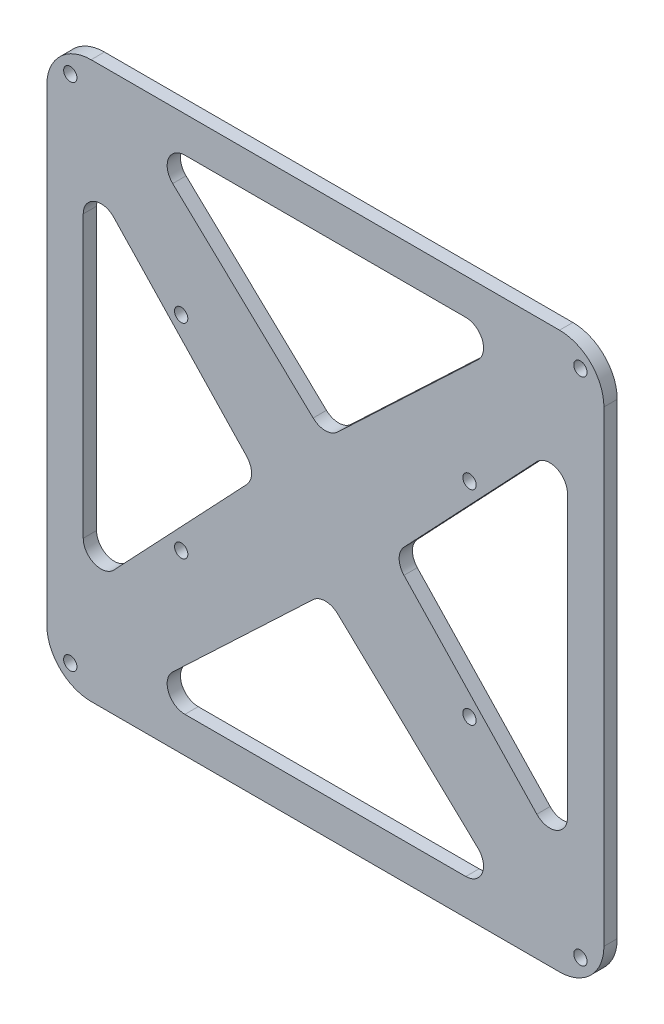
SolidWorks part; units mm, degrees
ref_plane "前视基准面" through (0, 0, 0) normal (0, 0, 1) x (1, 0, 0)
ref_plane "上视基准面" through (0, 0, 0) normal (0, 1, 0) x (1, 0, 0)
ref_plane "右视基准面" through (0, 0, 0) normal (1, 0, 0) x (0, 0, -1)
sketch "草图1" plane through (0, 0, 0) normal (0, 0, 1) x (1, 0, 0)
  line L0 (0, -62.65) -> (125.6, -62.65) construction
  line L1 (0, 0) -> (125.6, 0)
  line L2 (0, 0) -> (0, -125.3)
  line L3 (0, -125.3) -> (125.6, -125.3)
  line L4 (125.6, 0) -> (125.6, -125.3)
  line L5 (62.8, 0) -> (62.8, -125.3) construction
  line L6 (21.0898, -117.2294) -> (104.5102, -117.2294)
  line L7 (30.3, -85.65) -> (95.3, -85.65) construction
  line L8 (30.3, -85.65) -> (30.3, -39.65) construction
  line L9 (30.3, -39.65) -> (95.3, -39.65) construction
  line L10 (95.3, -85.65) -> (95.3, -39.65) construction
  line L11 (30.3, -85.65) -> (95.3, -39.65) construction
  line L12 (30.3, -39.65) -> (95.3, -85.65) construction
  line L13 (104.5102, -117.2294) -> (62.8, -77.7781)
  line L14 (62.8, -77.7781) -> (21.0898, -117.2294)
  line L15 (8.2206, -104.3602) -> (47.6719, -62.65)
  line L16 (8.2206, -20.9398) -> (8.2206, -104.3602)
  line L17 (47.6719, -62.65) -> (8.2206, -20.9398)
  line L18 (21.0898, -8.0706) -> (62.8, -47.5219)
  line L19 (104.5102, -8.0706) -> (21.0898, -8.0706)
  line L20 (62.8, -47.5219) -> (104.5102, -8.0706)
  line L21 (117.3794, -20.9398) -> (77.9281, -62.65)
  line L22 (117.3794, -104.3602) -> (117.3794, -20.9398)
  line L23 (77.9281, -62.65) -> (117.3794, -104.3602)
  line L25 (120.3, -5.15) -> (5.3, -5.15) construction
  line L26 (120.3, -5.15) -> (120.3, -120.15) construction
  line L27 (120.3, -120.15) -> (5.3, -120.15) construction
  line L28 (5.3, -5.15) -> (5.3, -120.15) construction
  line L29 (120.3, -5.15) -> (5.3, -120.15) construction
  line L30 (120.3, -120.15) -> (5.3, -5.15) construction
  circle A0 centre (30.3, -39.65) radius 1.5
  circle A1 centre (95.3, -39.65) radius 1.5
  circle A2 centre (95.3, -85.65) radius 1.5
  circle A3 centre (30.3, -85.65) radius 1.5
  circle A4 centre (120.3, -120.15) radius 1.5
  circle A5 centre (5.3, -120.15) radius 1.5
  circle A6 centre (5.3, -5.15) radius 1.5
  circle A7 centre (120.3, -5.15) radius 1.5
  point P9 (62.8, -62.65)
  point P22 (62.8, -117.2294)
  point P41 (62.8, -62.65)
  dimension "D5" = 3
  dimension "D6" = 3
  dimension "D7" = 3
  dimension "D8" = 3
  dimension "D12" = 3
  dimension "D13" = 3
  dimension "D14" = 3
  dimension "D15" = 3
  dimension "D1" = 125.3
  dimension "D2" = 125.6
  dimension "D3" = 65
  dimension "D4" = 46
  dimension "D10" = 115
  dimension "D11" = 115
  dimension "D9" = 4
extrude "凸台-拉伸1" add sketch "草图1" along normal blind 3
fillet "圆角1" radius 10 4 edges at (0, -125.3, 1.5) (125.6, -125.3, 1.5) (125.6, 0, 1.5) (0, 0, 1.5)
fillet "圆角2" radius 4 12 edges at (77.9281, -62.65, 1.5) (117.3794, -104.3602, 1.5) (104.5102, -117.2294, 1.5) (104.5102, -8.0706, 1.5) (117.3794, -20.9398, 1.5) (21.0898, -8.0706, 1.5) (62.8, -47.5219, 1.5) (8.2206, -104.3602, 1.5) (47.6719, -62.65, 1.5) (8.2206, -20.9398, 1.5) (62.8, -77.7781, 1.5) (21.0898, -117.2294, 1.5)
